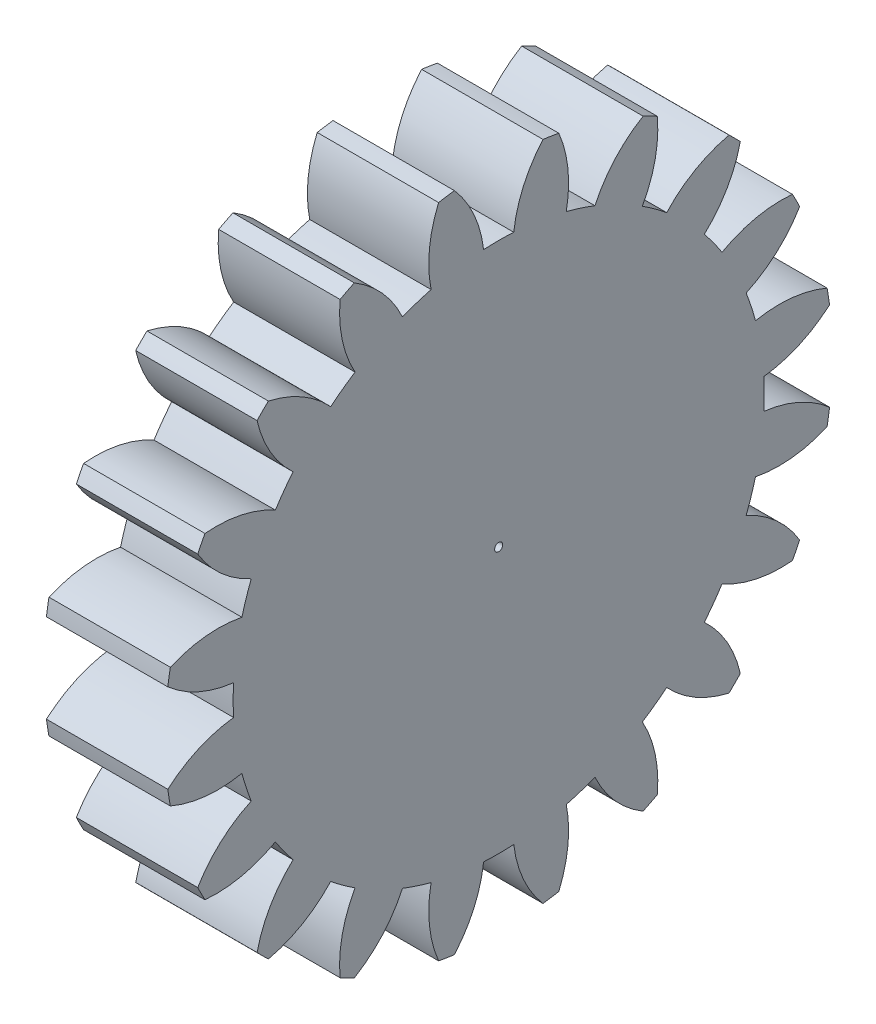
SolidWorks part; units mm, degrees
ref_plane "Plane1" through (0, 0, 0) normal (0, 0, 1) x (1, 0, 0)
ref_plane "Plane2" through (0, 0, 0) normal (0, 1, 0) x (1, 0, 0)
ref_plane "Plane3" through (0, 0, 0) normal (1, 0, 0) x (0, 0, -1)
sketch "HoldingSke" plane through (0, 0, 0) normal (0, 1, 0) x (1, 0, 0)
  line L0 (0, 0) -> (0.3132, -0.114)
  line L1 (-15, 0) -> (100, 0) construction
  line L2 (0, 0) -> (-2.1039, 2.3779)
  line L3 (0, 0) -> (-11.863, 4.5341)
  line L4 (0, 0) -> (8.1152, 2.9537)
  line L5 (0, 0) -> (-46.8476, -17.4728)
  line L6 (0, 0) -> (-9.9476, -6.7116)
  line L7 (-2.1039, 2.3779) -> (8.6586, 51.2059)
  line L8 (-76.2, 54.61) -> (-76.1, 54.61)
  line L9 (-71.009, 38.7566) -> (-53.1078, 45.2721)
  line L10 (-76.2, 71.12) -> (104.1128, 71.12)
  line L11 (0, 0) -> (-12, 0)
  line L12 (-76.2, 101.6) -> (-76.093, 101.6)
  line L13 (24.9733, 27.94) -> (52.9518, 28.4284)
  line L14 (24.9733, 27.94) -> (24.9743, 27.94)
  line L15 (24.9733, 27.94) -> (100.4006, 29.5858)
  line L16 (-63.627, -3) -> (-12.827, -3)
  circle A0 centre (0, 0) radius 0.4
  circle A1 centre (0, 0) radius 26.249
  circle A2 centre (0, 0) radius 37.5
  circle A3 centre (0, 0) radius 0.4
  dimension "MHD" = 52.498
  dimension "Hub_dia" = 75
  dimension "Bore" = 0.8
  dimension "MBD" = 0.8
  dimension "Num_teeth" = 20
  dimension "Pitch" = 0.3333
  dimension "Overall_len" = 50
  dimension "Show_teeth" = 20
  dimension "Thickness" = 12
  dimension "OAL" = 50.0001
  dimension "T_dim" = 0.1
  dimension "Ap" = 20
  dimension "H" = 19.05
  dimension "Pitch_radius" = 180.3128
  dimension "Width" = 12
  dimension "Backlash" = 0.107
  dimension "Addendum_fac" = 1
  dimension "Dedendum_fac" = 1.25
  dimension "Clearance_fac" = 0.25
  dimension "Dedendum_add" = 0.001
  dimension "Module" = 3
sketch "BasProSke" plane through (0, 0, 0) normal (0, 1, 0) x (1, 0, 0)
  line L0 (-10, 0) -> (60, 0) construction
  line L1 (0, 0) -> (0, 33)
  line L2 (0, 0) -> (12, 0)
  line L3 (12, 0) -> (12, 33)
  line L4 (12, 33) -> (0, 33)
  dimension "Thickness" = 12
  dimension "Diameter" = 66
revolve "Base-Revolve" add sketch "BasProSke" angle 360 about L0
sketch "TooCutSke" plane through (0, 0, 0) normal (1, 0, 0) x (0, 0, -1)
  line L1 (0, 0) -> (0, 107) construction
  line L2 (0, 0) -> (-2.5409, 29.8922) construction
  line L3 (0, 0) -> (-9.3616, 59.1066) construction
  line L4 (-2.5409, 29.8922) -> (-4.6808, 29.5533) construction
  arc A0 (1.4893, 26.2067) -> (-1.4893, 26.2067) centre (0, 0) ccw
  arc A1 (4.4016, 32.7308) -> (-4.4016, 32.7308) centre (0, 0) ccw
  circle A2 centre (0, 0) radius 30 construction
  circle A3 centre (0, 0) radius 28.1908 construction
  arc A4 (-1.4893, 26.2067) -> (-4.4016, 32.7308) centre (-13.4064, 24.799) ccw
  arc A5 (4.4016, 32.7308) -> (1.4893, 26.2067) centre (13.4064, 24.799) ccw
  dimension "Root_dia" = 52.498
  dimension "Overcut_dia" = 66.0508
  dimension "Pitch_dia" = 60
  dimension "Base_dia" = 56.3816
  dimension "Flank_rad" = 12
  dimension "Half_ang" = 9
  dimension "Half_CT" = 2.1665
extrude "ToothCut" cut sketch "TooCutSke" along normal through all
fillet "Breaks" [suppressed] radius 0.06
fillet "RootFillets" [suppressed] radius 0.751
pattern_circular "TeethCuts" count 20 every 18 about axis through (-10, 0, 0) along (1, 0, 0) of "ToothCut", "RootFillets", "Breaks"
sketch "HubNeaOneSke" plane through (0, 0, 0) normal (-1, 0, 0) x (0, 0, 1)
  circle A0 centre (0, 0) radius 26.249
  dimension "Diameter" = 52.498
extrude "HubNearOne" [suppressed] add sketch "HubNeaOneSke" along normal blind 38.0001
sketch "HubNeaBotSke" plane through (0, 0, 0) normal (-1, 0, 0) x (0, 0, 1)
  circle A0 centre (0, 0) radius 26.249
  dimension "Diameter" = 52.498
extrude "HubNearBoth" [suppressed] add sketch "HubNeaBotSke" along normal blind 19
ref_plane "FarPln" through (12, 0, 0) normal (1, 0, 0) x (0, 0, -1)
sketch "HubFarSke" plane through (12, 0, 0) normal (1, 0, 0) x (0, 0, -1)
  circle A0 centre (0, 0) radius 26.249
  dimension "Diameter" = 52.498
extrude "HubFar" [suppressed] add sketch "HubFarSke" along normal blind 19
sketch "BorSke" plane through (0, 0, 0) normal (1, 0, 0) x (0, 0, -1)
  circle A0 centre (0, 0) radius 0.4
  dimension "Diameter" = 0.8
extrude "Bore" cut sketch "BorSke" along normal mid plane 100.0001
sketch "KeySke" plane through (0, 0, 0) normal (1, 0, 0) x (0, 0, -1)
  line L0 (-0.05, 0) -> (-0.05, 0.5)
  line L1 (-0.05, 0.5) -> (0.05, 0.5)
  line L2 (0.05, 0.5) -> (0.05, 0)
  line L3 (0, 0) -> (0, 34) construction
  line L4 (-0.05, 0) -> (0.05, 0)
  dimension "Offset" = 0.5
  dimension "Width" = 0.1
extrude "Keyway" [suppressed] cut sketch "KeySke" along normal mid plane 100.0001
pattern_circular "Keyway2" [suppressed] count 2 every 90 about axis through (-10, 0, 0) along (1, 0, 0)
equation "' \"Module@HoldingSke\" = 6.35"
equation "' \"Num_teeth@HoldingSke\" = 12"
equation "' \"Ap@HoldingSke\" =  20"
equation "' \"Ap@HoldingSke\" = 20"
equation "' \"Width@HoldingSke\" = 0.5 * 25.4"
equation "' \"Hub_dia@HoldingSke\"= 1 * 25.4"
equation "' \"Hub_dia@HoldingSke\" = 1 * 25.4"
equation "' \"Overall_len@HoldingSke\" = 1.0 * 25.4"
equation "' \"Bore@HoldingSke\" = 0.75 * 25.4"
equation "' \"T_dim@HoldingSke\" = 0.1 * 25.4"
equation "' \"Width@KeySke\" = 0.25 * 25.4"
equation "' \"Show_teeth@HoldingSke\" = 13"
equation "' \"Backlash@HoldingSke\" = 0.009 * 25.4"
equation "' \"Addendum_fac@HoldingSke\" = 1.0"
equation "' \"Dedendum_fac@HoldingSke\" = 1.25"
equation "' \"Dedendum_add@HoldingSke\" = 0.00005 * 25.4"
equation "' \"Clearance_fac@HoldingSke\" = 0.25"
equation "\"Pitch@HoldingSke\" = 1 / \"Module@HoldingSke\""
equation "\"Overcut_dia@TooCutSke\" = (\"Num_teeth@HoldingSke\" + 2 * \"Addendum_fac@HoldingSke\") / \"Pitch@HoldingSke\" + 0.002 * 25.4"
equation "\"Pitch_dia@TooCutSke\" = \"Num_teeth@HoldingSke\" / \"Pitch@HoldingSke\""
equation "\"Base_dia@TooCutSke\" = \"Num_teeth@HoldingSke\" / \"Pitch@HoldingSke\" * cos((\"Ap@HoldingSke\"  * 3.14159265 / 180))"
equation "\"Root_dia@TooCutSke\" = (\"Num_teeth@HoldingSke\" + 2) / \"Pitch@HoldingSke\" - 2 * (\"Addendum_fac@HoldingSke\" + \"Dedendum_fac@HoldingSke\") / \"Pitch@HoldingSke\" - \"Dedendum_add@HoldingSke\" * 2"
equation "\"Half_ang@TooCutSke\" = 180 / \"Num_teeth@HoldingSke\""
equation "\"Half_CT@TooCutSke\" = \"Num_teeth@HoldingSke\" / \"Pitch@HoldingSke\" * sin((3.14159265 / 2 / \"Num_teeth@HoldingSke\")) / 2 - 7 * \"Backlash@HoldingSke\" / 4"
equation "\"Flank_rad@TooCutSke\" = \"Num_teeth@HoldingSke\" / \"Pitch@HoldingSke\" / 5"
equation "\"Radius@RootFillets\" = \"Clearance_fac@HoldingSke\" / \"Pitch@HoldingSke\" + \"Dedendum_add@HoldingSke\""
equation "\"Break_rad@Breaks\" = 0.02 / \"Pitch@HoldingSke\""
equation "\"Thickness@HoldingSke\" = \"Width@HoldingSke\""
equation "\"OAL@HoldingSke\" = \"Thickness@HoldingSke\""
equation "\"MHD@HoldingSke\" = (\"Num_teeth@HoldingSke\" + 2) / \"Pitch@HoldingSke\" - 2 * (\"Addendum_fac@HoldingSke\" + \"Dedendum_fac@HoldingSke\")  / \"Pitch@HoldingSke\" - \"Dedendum_add@HoldingSke\" * 2"
equation "\"MBD@HoldingSke\" = (\"Num_teeth@HoldingSke\" + 2) / \"Pitch@HoldingSke\" - 2 * (\"Addendum_fac@HoldingSke\" + \"Dedendum_fac@HoldingSke\")  / \"Pitch@HoldingSke\" - \"Dedendum_add@HoldingSke\" * 2 - 0.002 * 25.4"
equation "\"MHD@HoldingSke\" = ((sgn( \"MHD@HoldingSke\" - \"Hub_dia@HoldingSke\" )-1)*( \"MHD@HoldingSke\" - \"Hub_dia@HoldingSke\" ))/-2+ \"Hub_dia@HoldingSke\""
equation "\"MBD@HoldingSke\" = ((sgn( \"MBD@HoldingSke\" - \"Bore@HoldingSke\" )-1)*( \"MBD@HoldingSke\" - \"Bore@HoldingSke\" ))/-2+ \"Bore@HoldingSke\""
equation "\"OAL@HoldingSke\" = ((sgn( \"OAL@HoldingSke\" - \"Overall_len@HoldingSke\" )+1)*( \"OAL@HoldingSke\" - \"Overall_len@HoldingSke\" ))/2 + \"Overall_len@HoldingSke\" + 0.000002 * 25.4"
equation "\"Num_teeth@TeethCuts\" = int( \"Show_teeth@HoldingSke\" ) + 1"
equation "\"Num_teeth@TeethCuts\" = ((sgn( \"Num_teeth@TeethCuts\" - \"Num_teeth@HoldingSke\" )-1)*( \"Num_teeth@TeethCuts\" - \"Num_teeth@HoldingSke\" ))/-2+ \"Num_teeth@HoldingSke\""
equation "\"Num_teeth@TeethCuts\" = ((sgn( \"Num_teeth@TeethCuts\" - 2.0)+1)*( \"Num_teeth@TeethCuts\" - 2.0))/2 +2.0"
equation "\"Angle@TeethCuts\" = 360.0 / \"Num_teeth@HoldingSke\""
equation "\"Diameter@BasProSke\" = (\"Num_teeth@HoldingSke\" + 2 * \"Addendum_fac@HoldingSke\") / \"Pitch@HoldingSke\""
equation "\"Thickness@BasProSke\"  = \"Thickness@HoldingSke\""
equation "' \"Fillet_rad@BasProSke\" =  \"Thickness@HoldingSke\" * 0.05"
equation "' \"Fillet_rad@BasProSke\" = \"Thickness@HoldingSke\" * 0.05"
equation "\"MHD@HoldingSke\" = ((sgn( \"MHD@HoldingSke\" - \"Root_dia@TooCutSke\" )-1)*( \"MHD@HoldingSke\" - \"Root_dia@TooCutSke\" ))/-2+ \"Root_dia@TooCutSke\""
equation "\"Diameter@HubNeaOneSke\" = \"MHD@HoldingSke\""
equation "\"Length@HubNearOne\" = \"OAL@HoldingSke\" - \"Thickness@BasProSke\""
equation "\"Diameter@HubNeaBotSke\" = \"MHD@HoldingSke\""
equation "\"Length@HubNearBoth\" = ( \"OAL@HoldingSke\" - \"Thickness@BasProSke\" ) / 2.0"
equation "\"Thickness@FarPln\" = \"Thickness@BasProSke\""
equation "\"Diameter@HubFarSke\" = \"MHD@HoldingSke\""
equation "\"Length@HubFar\" = ( \"OAL@HoldingSke\" - \"Thickness@BasProSke\" ) / 2.0"
equation "\"Diameter@BorSke\" = \"MBD@HoldingSke\""
equation "\"D1@Bore\" = \"OAL@HoldingSke\" * 2.0"
equation "\"D1@Keyway\" = \"OAL@HoldingSke\" * 2.0"
equation "\"Offset@KeySke\" = \"T_dim@HoldingSke\" + \"MBD@HoldingSke\" / 2.0"
